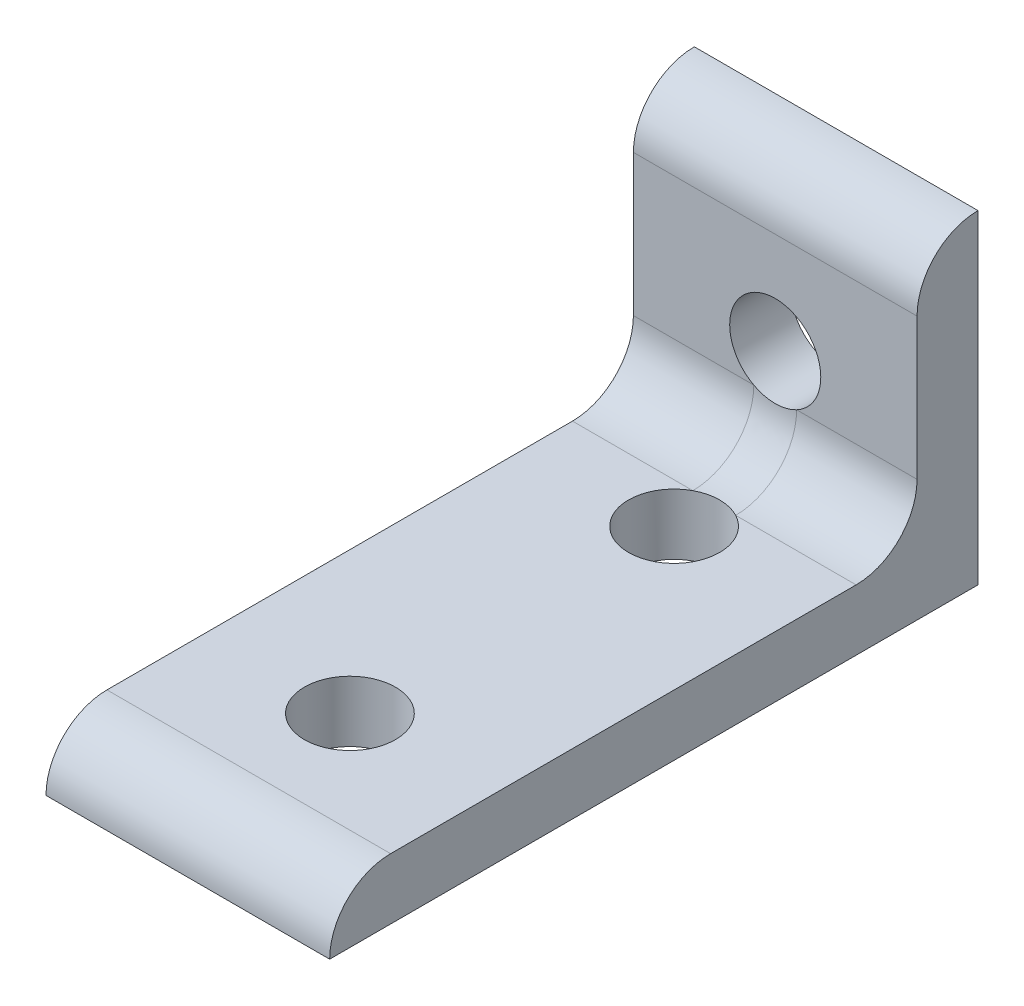
SolidWorks part; units mm, degrees
material "6061 Alloy"
ref_plane "Front Plane" through (0, 0, 0) normal (0, 0, 1) x (1, 0, 0)
ref_plane "Top Plane" through (0, 0, 0) normal (0, 1, 0) x (1, 0, 0)
ref_plane "Right Plane" through (0, 0, 0) normal (1, 0, 0) x (0, 0, -1)
sketch "Sketch1" plane through (0, 0, 0) normal (1, 0, 0) x (0, 0, -1)
  line L0 (-28.1992, 21.8977) -> (22.6008, 21.8977)
  line L1 (22.6008, 21.8977) -> (17.8256, 26.6729)
  line L2 (-23.424, 26.6729) -> (17.8256, 26.6729)
  line L3 (-28.1992, 26.6729) -> (22.6008, 26.6729) construction
  arc A0 (-23.424, 26.6729) -> (-28.1992, 21.8977) centre (-23.424, 21.8977) ccw
  dimension "D1" = 4.7752
extrude "Extrude1" add sketch "Sketch1" along normal blind 22.225
sketch "Sketch2" plane through (0, 26.6729, 0) normal (0, 1, 0) x (1, 0, 0)
  circle A0 centre (11.1125, -15.4992) radius 3.5687
  circle A1 centre (11.1125, 9.9008) radius 3.5687
extrude "Cut-Extrude1" cut sketch "Sketch2" against normal through all
mirror "Mirror1" about plane through (22.225, 21.8977, -22.6008) normal (0, -0.7071, 0.7071) of bodies 102
fillet "Fillet1" radius 4.7752 1 edges at (11.1125, 26.6729, -17.8256)
sketch "Sketch3" plane through (22.225, 0, 0) normal (1, 0, 0) x (0, 0, -1)
  line L0 (22.6008, 21.8977) -> (22.6008, 47.2977)
  line L1 (22.6008, 72.6977) -> (22.6008, 21.8977) construction
  line L2 (17.8256, 42.5225) -> (16.9273, 73.2505)
  line L3 (16.9273, 73.2505) -> (23.8519, 73.8324)
  line L4 (23.8519, 73.8324) -> (22.6008, 47.2977)
  arc A0 (22.6008, 47.2977) -> (17.8256, 42.5225) centre (22.6008, 42.5225) ccw
  line M3 (22.6008, 21.8977) -> (22.6008, 72.6977)
  arc M4 (22.6008, 72.6977) -> (17.8256, 67.9225) centre (22.6008, 67.9225) ccw
  line M5 (17.8256, 67.9225) -> (17.8256, 31.4481)
extrude "Cut-Extrude2" cut sketch "Sketch3" against normal through all contours A0 M3 M4 M5
